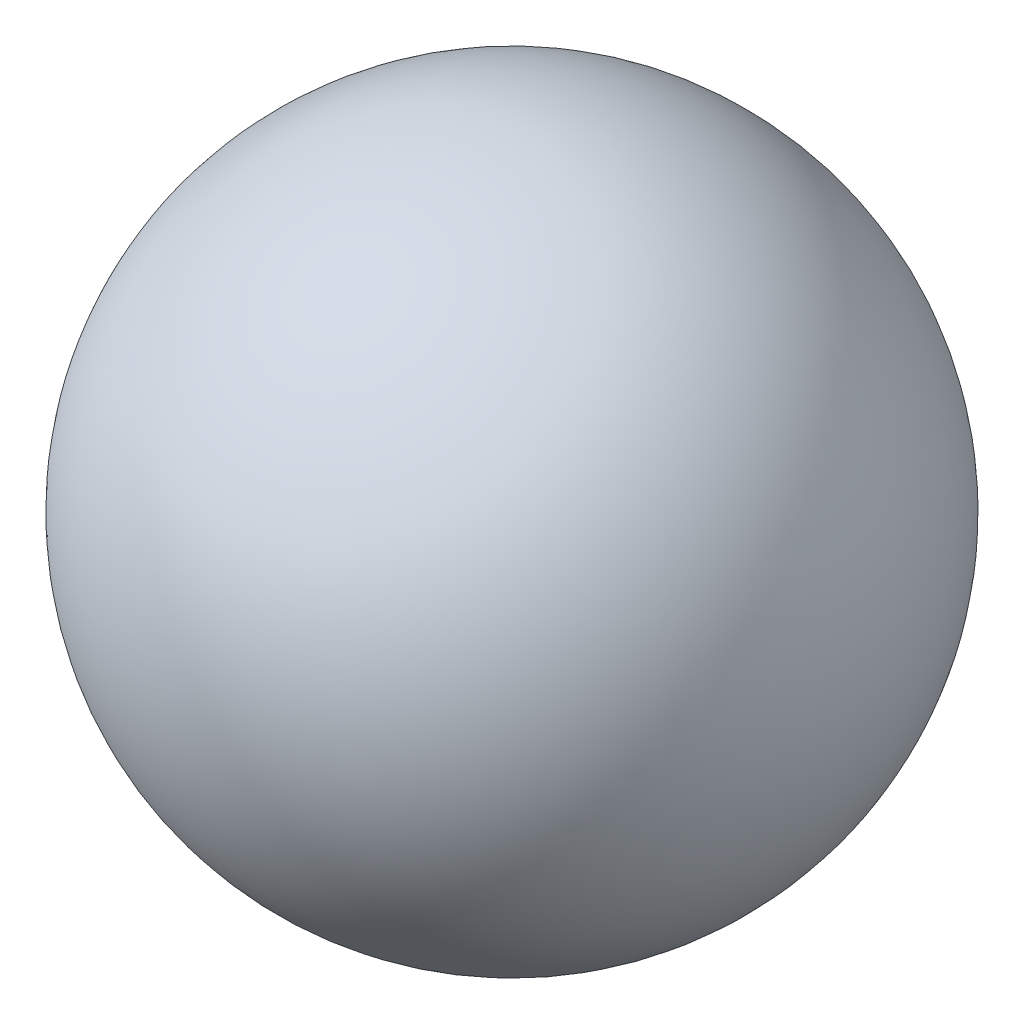
SolidWorks part; units mm, degrees
ref_plane "Front Plane" through (0, 0, 0) normal (0, 0, 1) x (1, 0, 0)
ref_plane "Top Plane" through (0, 0, 0) normal (0, 1, 0) x (1, 0, 0)
ref_plane "Right Plane" through (0, 0, 0) normal (1, 0, 0) x (0, 0, -1)
ref_plane "Plane1" through (0, 0, 0) normal (0, 0, 1) x (1, 0, 0)
sketch "Sketch1" plane through (0, 0, 0) normal (0, 0, 1) x (1, 0, 0)
  line L0 (4.5875, 9) -> (1.4125, 9)
  line L1 (4.5875, 9) -> (1.4125, 9) construction
  arc A0 (1.4125, 9) -> (4.5875, 9) centre (3, 9) cw
revolve "Revolve1" add sketch "Sketch1" angle 360 about L1
